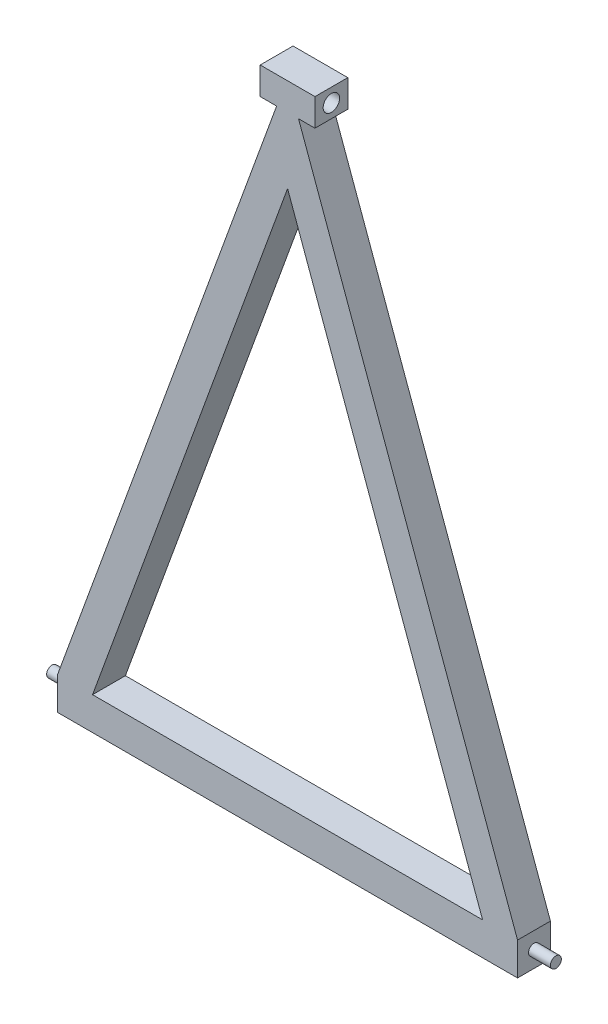
SolidWorks part; units mm, degrees
ref_plane "Front Plane" through (0, 0, 0) normal (0, 0, 1) x (1, 0, 0)
ref_plane "Top Plane" through (0, 0, 0) normal (0, 1, 0) x (1, 0, 0)
ref_plane "Right Plane" through (0, 0, 0) normal (1, 0, 0) x (0, 0, -1)
sketch "Sketch1" plane through (0, 0, 0) normal (0, 0, 1) x (1, 0, 0)
  line L0 (0, 0) -> (533.4, 0)
  line L1 (533.4, 0) -> (533.4, 76.2)
  line L2 (533.4, 76.2) -> (25.4, 1471.9185)
  line L3 (25.4, 1471.9185) -> (63.5, 1471.9185)
  line L4 (63.5, 1471.9185) -> (63.5, 1535.4185)
  line L5 (63.5, 1535.4185) -> (-63.5, 1535.4185)
  line L6 (-63.5, 1535.4185) -> (-63.5, 1471.9185)
  line L7 (-63.5, 1471.9185) -> (-25.4, 1471.9185)
  line L8 (-25.4, 1471.9185) -> (-533.4, 76.2)
  line L9 (-533.4, 76.2) -> (-533.4, 0)
  line L10 (-533.4, 0) -> (0, 0)
  line L11 (-452.3097, 76.2) -> (452.3097, 76.2)
  line L12 (452.3097, 76.2) -> (0, 1318.9106)
  line L13 (0, 1318.9106) -> (-452.3097, 76.2)
  dimension "D1" = 533.4
  dimension "D2" = 533.4
  dimension "D3" = 76.2
  dimension "D4" = 38.1
  dimension "D5" = 38.1
  dimension "D6" = 127
  dimension "D7" = 63.5
  dimension "D8" = 40
  dimension "D9" = 76.2
  dimension "D10" = 76.2
extrude "Boss-Extrude1" add sketch "Sketch1" along normal blind 76.2
sketch "Sketch2" plane through (63.5, 0, 0) normal (1, 0, 0) x (0, 0, -1)
  line L0 (0, 1471.9185) -> (0, 1535.4185) construction
  line L2 (-76.2, 1535.4185) -> (0, 1535.4185) construction
  circle A0 centre (-38.1, 1503.6685) radius 19.05
  dimension "D1" = 38.1
  dimension "D3" = 38.1
  dimension "D2" = 31.75
extrude "Cut-Extrude1" cut sketch "Sketch2" against normal blind 140.97
sketch "Sketch3" plane through (-533.4, 0, 0) normal (-1, 0, 0) x (0, 0, 1)
  line L0 (76.2, 76.2) -> (0, 76.2) construction
  line L1 (76.2, 76.2) -> (76.2, 0) construction
  circle A0 centre (38.1, 38.1) radius 12.7
  point P2 (38.1, 76.2)
  point P5 (76.2, 38.1)
  dimension "D1" = 38.1
  dimension "D3" = 25.4
  dimension "D2" = 38.1
extrude "Boss-Extrude2" add sketch "Sketch3" along normal blind 50.8
sketch "Sketch4" plane through (533.4, 0, 0) normal (1, 0, 0) x (0, 0, -1)
  line L0 (-76.2, 76.2) -> (0, 76.2) construction
  line L1 (0, 0) -> (0, 76.2) construction
  circle A0 centre (-38.1, 38.1) radius 12.7
  point P4 (0, 38.1)
  dimension "D1" = 38.1
  dimension "D3" = 25.4
  dimension "D2" = 38.1
extrude "Boss-Extrude3" add sketch "Sketch4" along normal blind 50.8
